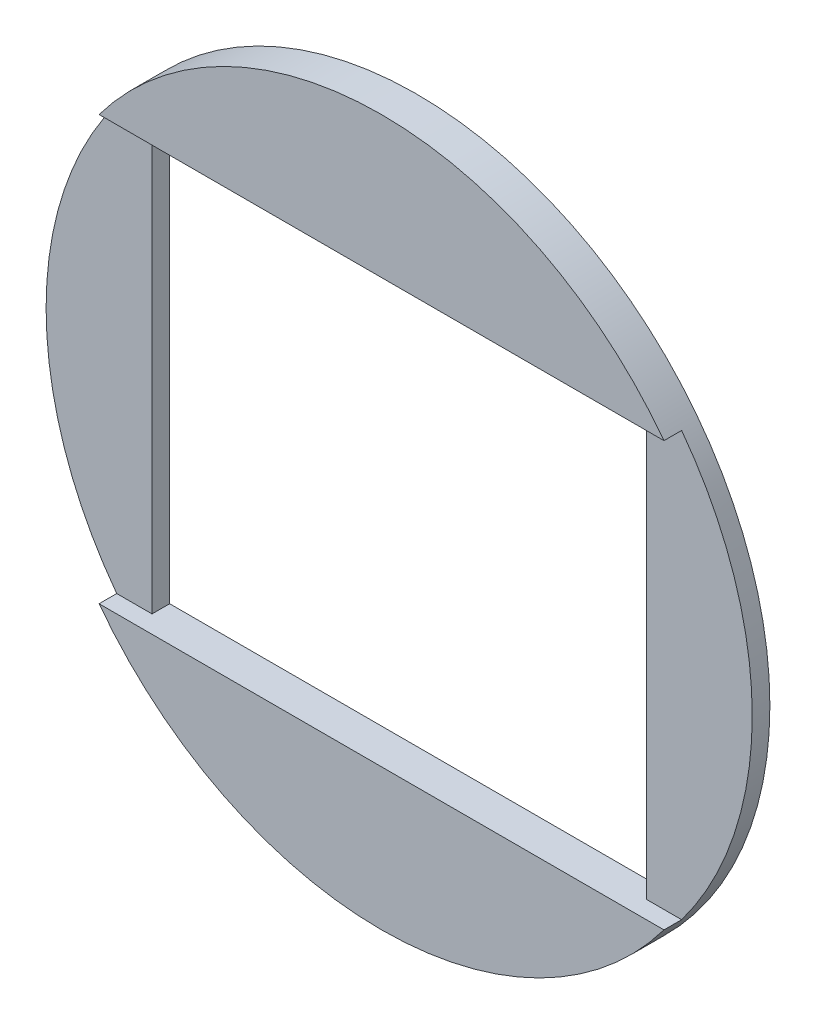
SolidWorks part; units mm, degrees
material "Polyester Resin"
ref_plane "Front Plane" through (0, 0, 0) normal (0, 0, 1) x (1, 0, 0)
ref_plane "Top Plane" through (0, 0, 0) normal (0, 1, 0) x (1, 0, 0)
ref_plane "Right Plane" through (0, 0, 0) normal (1, 0, 0) x (0, 0, -1)
sketch "Sketch1" plane through (0, 0, 0) normal (0, 0, 1) x (1, 0, 0)
  line L1 (100.8733, -4.3988) -> (50.0733, -4.3988)
  line L2 (100.8733, -4.3988) -> (100.8733, -42.4988)
  line L3 (100.8733, -42.4988) -> (50.0733, -42.4988)
  line L4 (50.0733, -4.3988) -> (50.0733, -42.4988)
  line L5 (-22.225, -19.05) -> (22.225, -19.05)
  line L6 (-22.225, -19.05) -> (-22.225, 19.05)
  line L7 (-22.225, 19.05) -> (22.225, 19.05)
  line L8 (22.225, -19.05) -> (22.225, 19.05)
  line L9 (-22.225, -19.05) -> (22.225, 19.05) construction
  line L10 (-22.225, 19.05) -> (22.225, -19.05) construction
  circle A0 centre (0, 0) radius 31.75
  point P2 (0, 0)
  point P8 (31.75, 0)
  point P9 (31.75, 0)
  dimension "D1" = 38.1
  dimension "D2" = 63.5
  dimension "D3" = 50.8
  dimension "D4" = 38.1
  dimension "D5" = 44.45
extrude "Base" add sketch "Sketch1" along normal mid plane 3.175 contours L1 A0 L3 L4
sketch "Sketch2" plane through (22.225, 0, 0) normal (-1, 0, 0) x (0, 0, 1)
  line L1 (0, 19.05) -> (1.5875, 19.05)
  line L2 (0, 19.05) -> (0, -19.05)
  line L3 (0, -19.05) -> (1.5875, -19.05)
  line L4 (1.5875, 19.05) -> (1.5875, -19.05)
  point P5 (0, 0)
extrude "Trench" cut sketch "Sketch2" against normal up to surface and the other way up to surface up to face at (31.75, 0, 1.5875) other way up to face at (31.75, 0, 1.5875)
